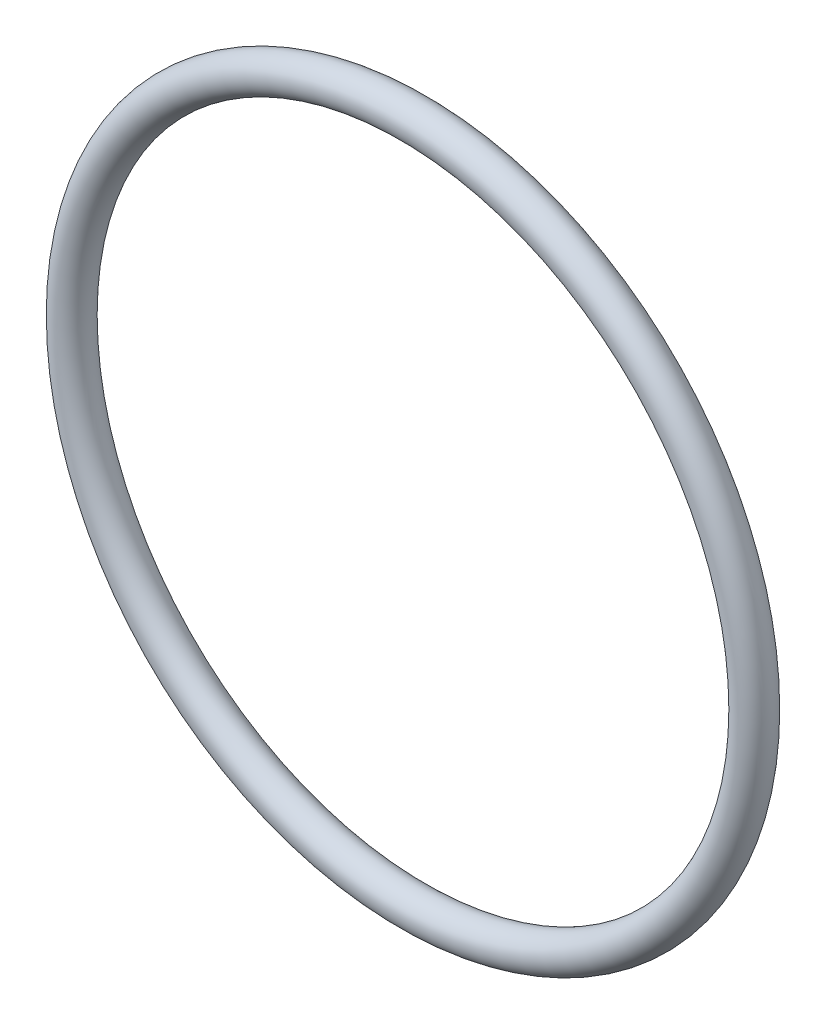
SolidWorks part; units mm, degrees
material "Rubber"
ref_plane "Front Plane" through (0, 0, 0) normal (0, 0, 1) x (1, 0, 0)
ref_plane "Top Plane" through (0, 0, 0) normal (0, 1, 0) x (1, 0, 0)
ref_plane "Right Plane" through (0, 0, 0) normal (1, 0, 0) x (0, 0, -1)
sketch "Sketch4" plane through (0, 0, 0) normal (0, 1, 0) x (1, 0, 0)
  circle A0 centre (0, 0) radius 1.3081
  dimension "D1" = 2.6162
ref_plane "Plane1" through (24.81, 0, 0) normal (1, 0, 0) x (0, 0, -1)
ref_axis "Axis1" through (24.81, 0, 1.4389) along (0, 0, -1)
revolve "Revolve2" add sketch "Sketch4" angle 360 about axis through (24.81, 0, 1.4389) along (0, 0, -1)
sketch "Sketch6" plane through (0, 0, 0) normal (0, 1, 0) x (1, 0, 0)
  circle A1 centre (0, 0) radius 1.3081
  circle A2 centre (0, 0) radius 1.3081 construction
  point P0 (0, 1.3081)
  dimension "D1" = 0
ref_plane "Plane2" through (0, 0, -1.3081) normal (0, 0, 1) x (1, 0, 0)
